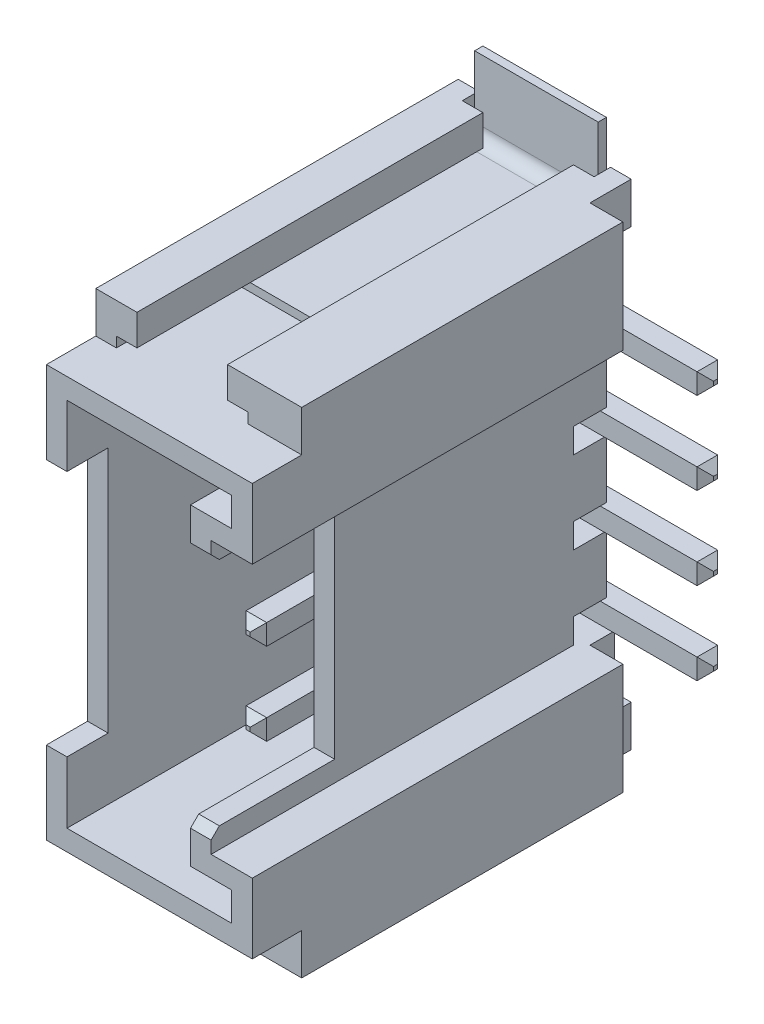
SolidWorks part; units mm, degrees
ref_plane "Plan de face" through (0, 0, 0) normal (0, 0, 1) x (1, 0, 0)
ref_plane "Plan de dessus" through (0, 0, 0) normal (0, 1, 0) x (1, 0, 0)
ref_plane "Plan de droite" through (0, 0, 0) normal (1, 0, 0) x (0, 0, -1)
sketch "Esquisse1" plane through (0, 0, 0) normal (0, 0, 1) x (1, 0, 0)
  line L0 (0, 3.3) -> (0, 6)
  line L1 (0, 6) -> (-1.8, 6)
  line L2 (-1.8, 6) -> (-1.8, 5.25)
  line L3 (-1.8, 5.25) -> (-1.3, 5.25)
  line L4 (-1.3, 5.25) -> (-1.3, 5)
  line L5 (-1.3, 5) -> (-4.5, 5)
  line L6 (-4.5, 5) -> (-4.5, 5.25)
  line L7 (-4.5, 5.25) -> (-4, 5.25)
  line L8 (-4, 5.25) -> (-4, 6)
  line L9 (-4, 6) -> (-5, 6)
  line L10 (-5, 6) -> (-5, -6)
  line L11 (-1, -3.3) -> (0, -3.3)
  line L12 (-4, -6) -> (-5, -6)
  line L13 (-4, -5.25) -> (-4, -6)
  line L14 (-4.5, -5.25) -> (-4, -5.25)
  line L15 (-4.5, -5) -> (-4.5, -5.25)
  line L16 (-1.3, -5) -> (-4.5, -5)
  line L17 (-1.3, -5.25) -> (-1.3, -5)
  line L18 (-1.8, -5.25) -> (-1.3, -5.25)
  line L19 (-1.8, -6) -> (-1.8, -5.25)
  line L20 (0, -6) -> (-1.8, -6)
  line L21 (0, -3.3) -> (0, -6)
  line L22 (-1, -3.3) -> (-1, 3.3)
  line L23 (-1, 3.3) -> (0, 3.3)
  line L24 (-1, 0) -> (0, 0) construction
  dimension "D1" = 6
  dimension "D2" = 2.2
  dimension "D3" = 3.2
  dimension "D4" = 0.25
  dimension "D5" = 2.7
  dimension "D6" = 1
  dimension "D7" = 1
  dimension "D8" = 5
  dimension "D9" = 1
extrude "Boss.-Extru.1" add sketch "Esquisse1" along normal blind 10
sketch "Esquisse4" plane through (0, 0, 10) normal (0, 0, 1) x (1, 0, 0)
  line L1 (-0.5, 4.5) -> (-4.5, 4.5)
  line L2 (-4.5, 4.5) -> (-4.5, -4.5)
  line L3 (-4.5, -4.5) -> (-0.5, -4.5)
  line L4 (-5, 6) -> (-5, -6) construction
  line L5 (-1.3, 5) -> (-4.5, 5) construction
  line L20 (-0.5, -6) -> (-0.5, -3.8)
  line L21 (-0.5, -3.8) -> (-1.5, -3.8)
  line L22 (-0.5, 3.8) -> (-0.5, 6)
  line L23 (-1.5, 3.8) -> (-0.5, 3.8)
  line L24 (-1.5, -3.8) -> (-1.5, 3.8)
  line L25 (-0.5, -4.5) -> (-0.5, -3.8)
  line L26 (-0.5, -3.8) -> (-1.5, -3.8)
  line L27 (-0.5, 3.8) -> (-0.5, 4.5)
  line L28 (-1.5, 3.8) -> (-0.5, 3.8)
  line L29 (-1.5, -3.8) -> (-1.5, 3.8)
  dimension "D2" = 0.5
  dimension "D3" = 0.5
  dimension "D1" = 0.5
extrude "Enlèv. mat.-Extru.1" cut sketch "Esquisse4" against normal blind 6.5
sketch "Esquisse5" plane through (-4.5, 0, 0) normal (1, 0, 0) x (0, 0, -1)
  line L0 (-10, 4.5) -> (-10, -4.5) construction
  line L1 (-11, -3) -> (-9, -3)
  line L2 (-11, -3) -> (-11, 3)
  line L3 (-11, 3) -> (-9, 3)
  line L4 (-9, -3) -> (-9, 3)
  line L5 (-11, -3) -> (-9, 3) construction
  line L6 (-11, 3) -> (-9, -3) construction
  point P0 (-10, 0)
  dimension "D1" = 1
  dimension "D2" = 2
extrude "Enlèv. mat.-Extru.2" cut sketch "Esquisse5" against normal through all
sketch "Esquisse6" plane through (-1.5, 0, 0) normal (-1, 0, 0) x (0, 0, 1)
  line L0 (10, -3.8) -> (10, 3.8) construction
  line L1 (13, 2.8) -> (7, 2.8)
  line L2 (13, 2.8) -> (13, -2.8)
  line L3 (13, -2.8) -> (7, -2.8)
  line L4 (7, 2.8) -> (7, -2.8)
  line L5 (13, 2.8) -> (7, -2.8) construction
  line L6 (13, -2.8) -> (7, 2.8) construction
  point P0 (10, 0)
  dimension "D1" = 3
  dimension "D2" = 2.2
extrude "Enlèv. mat.-Extru.3" cut sketch "Esquisse6" against normal through all
chamfer "Chanfrein1" distance 0.2 angle 45 2 edges at (-1.25, -2.8, 10) (-1.25, 2.8, 10)
sketch "Esquisse7" plane through (-5, 0, 0) normal (-1, 0, 0) x (0, 0, 1)
  line L0 (10, 6) -> (0, 6) construction
  line L1 (10, 5) -> (8.8, 5)
  line L2 (10, 5) -> (10, 6)
  line L3 (10, 6) -> (8.8, 6)
  line L4 (8.8, 5) -> (8.8, 6)
  line L6 (10, -6) -> (0, -6) construction
  line L7 (10, -5) -> (8.8, -5)
  line L8 (10, -5) -> (10, -6)
  line L9 (10, -6) -> (8.8, -6)
  line L10 (8.8, -5) -> (8.8, -6)
  line L12 (0, 5) -> (0.4, 5)
  line L13 (0, 6) -> (0, -6) construction
  line L14 (0.4, 5) -> (0.4, 3.3)
  line L15 (0.4, 3.3) -> (1.2, 3.3)
  line L16 (1.2, 3.3) -> (1.2, 2.7)
  line L17 (1.2, 2.7) -> (0.4, 2.7)
  line L18 (0.4, 2.7) -> (0.4, 1.3)
  line L19 (0.4, 1.3) -> (1.2, 1.3)
  line L20 (1.2, 1.3) -> (1.2, 0.7)
  line L21 (1.2, 0.7) -> (0.4, 0.7)
  line L22 (0.4, 0.7) -> (0.4, -0.7)
  line L23 (0.4, -0.7) -> (1.2, -0.7)
  line L24 (1.2, -0.7) -> (1.2, -1.3)
  line L25 (1.2, -1.3) -> (0.4, -1.3)
  line L26 (0.4, -1.3) -> (0.4, -2.7)
  line L27 (0.4, -2.7) -> (1.2, -2.7)
  line L28 (1.2, -2.7) -> (1.2, -3.3)
  line L29 (1.2, -3.3) -> (0.4, -3.3)
  line L30 (0.4, -3.3) -> (0.4, -5)
  line L31 (0.4, -5) -> (0, -5)
  line L32 (0, -5) -> (0, 5)
  point P7 (0, 0)
  dimension "D1" = 1.2
  dimension "D2" = 0.4
  dimension "D3" = 1
  dimension "D4" = 0.7
  dimension "D5" = 0.6
  dimension "D6" = 2
  dimension "D7" = 1.2
extrude "Enlèv. mat.-Extru.4" cut sketch "Esquisse7" against normal through all
sketch "Esquisse8" plane through (0, 6, 0) normal (0, 1, 0) x (1, 0, 0)
  line L0 (-4, 0) -> (-5, 0) construction
  line L1 (0, 0) -> (-0.8, 0)
  line L2 (0, 0) -> (0, -1)
  line L3 (0, -1) -> (-0.8, -1)
  line L4 (-0.8, 0) -> (-0.8, -1)
  line L5 (-4.5, 0) -> (-1.3, 0)
  line L6 (-4.5, 0) -> (-4.5, -0.4)
  line L7 (-4.5, -0.4) -> (-1.3, -0.4)
  line L8 (-1.3, 0) -> (-1.3, -0.4)
  dimension "D1" = 1
  dimension "D2" = 0.8
extrude "Enlèv. mat.-Extru.5" cut sketch "Esquisse8" against normal through all
sketch "Esquisse9" plane through (0, 0, 0) normal (0, 1, 0) x (1, 0, 0)
  line L0 (-2.9, -7.2) -> (-2.9, -0.75)
  line L1 (-2.4, -0.25) -> (1.5, -0.25)
  line L2 (-0.8, 0) -> (-1.3, 0) construction
  line L3 (-4.5, 0) -> (-4.5, -0.4) construction
  line L4 (0, -10) -> (-5, -10) construction
  line L5 (-5, -8.8) -> (-5, 0) construction
  arc A0 (-2.9, -0.75) -> (-2.4, -0.25) centre (-2.4, -0.75) cw
  dimension "D1" = 0.5
  dimension "D2" = 0.25
  dimension "D3" = 1.6
  dimension "D4" = 2.8
  dimension "D5" = 6.5
extrude "Extru.-Mince1" add sketch "Esquisse9" along normal mid plane 0.5 from offset 3 separate body thin thin type mid plane wall 0.5
chamfer "Chanfrein2" distance 0.2 angle 45 8 edges at (1.5, 3, 0.5) (1.5, 3.25, 0.25) (1.5, 3, 0) (1.5, 2.75, 0.25) (-3.15, 3, 7.2) (-2.9, 3.25, 7.2) (-2.65, 3, 7.2) (-2.9, 2.75, 7.2)
pattern_linear "Répétition linéaire1" count 4 spacing 2 along (0, -1, 0) of bodies 107
sketch "Esquisse10" plane through (-4.5, 0, 0) normal (1, 0, 0) x (0, 0, -1)
  line L0 (-6, 5) -> (-0.5, 5)
  line L1 (-8.8, 5) -> (-0.4, 5) construction
  line L2 (0, 5.5) -> (0, 7)
  line L3 (-8.8, 6) -> (-1, 6) construction
  line L5 (-10, 3.3) -> (-10, 5) construction
  arc A0 (-0.5, 5) -> (0, 5.5) centre (-0.5, 5.5) ccw
  point P13 (0, 5)
  dimension "D3" = 0.5
  dimension "D1" = 1
  dimension "D2" = 4
extrude "Extru.-Mince2" add sketch "Esquisse10" along normal blind 3 from offset 0.1 separate body thin thin type one direction reverse wall 0.2
mirror "Symétrie3" about plane through (0, 0, 0) normal (0, 1, 0) of bodies 111
